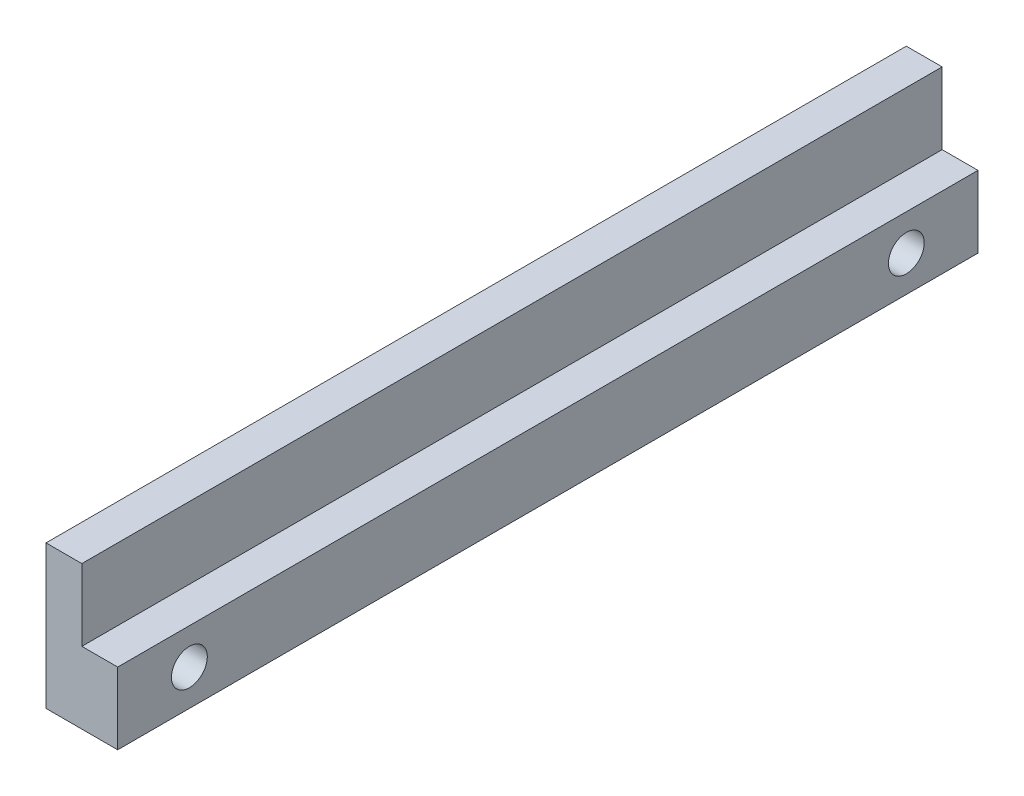
SolidWorks part; units mm, degrees
material "PBT General Purpose"
ref_plane "Front Plane" through (0, 0, 0) normal (0, 0, 1) x (1, 0, 0)
ref_plane "Top Plane" through (0, 0, 0) normal (0, 1, 0) x (1, 0, 0)
ref_plane "Right Plane" through (0, 0, 0) normal (1, 0, 0) x (0, 0, -1)
sketch "Sketch1" plane through (0, 0, 0) normal (0, 0, 1) x (1, 0, 0)
  line L0 (0, 12.7) -> (0, 0)
  line L1 (0, 0) -> (6.35, 0)
  line L2 (6.35, 0) -> (6.35, -12.7)
  line L3 (6.35, -12.7) -> (-6.35, -12.7)
  line L4 (-6.35, -12.7) -> (-6.35, 12.7)
  line L5 (-6.35, 12.7) -> (0, 12.7)
  dimension "D1" = 6.35
  dimension "D2" = 12.7
  dimension "D3" = 25.4
  dimension "D4" = 12.7
extrude "Boss-Extrude1" add sketch "Sketch1" along normal mid plane 152.4
sketch "Sketch2" plane through (-6.35, 0, 0) normal (-1, 0, 0) x (0, 0, 1)
  line L0 (-76.2, -12.7) -> (-76.2, 0) construction
  line L1 (0, 28.3768) -> (0, -26.4323) construction
  circle A1 centre (-63.5, -6.35) radius 3.175
  circle A2 centre (63.5, -6.35) radius 3.175
  point P7 (-76.2, -6.35)
  dimension "D1" = 6.35
  dimension "D2" = 12.7
extrude "Cut-Extrude1" cut sketch "Sketch2" against normal through all both and the other way through all
sketch "Sketch3" plane through (6.35, 0, 0) normal (1, 0, 0) x (0, 0, -1)
  line L0 (76.2, -12.7) -> (76.2, 0) construction
  circle A0 centre (0, -6.35) radius 3.175
  circle A1 centre (63.5, -6.35) radius 3.175 construction
  point P7 (76.2, -6.35)
extrude "Cut-Extrude2" [suppressed] cut sketch "Sketch3" against normal through all both and the other way through all
